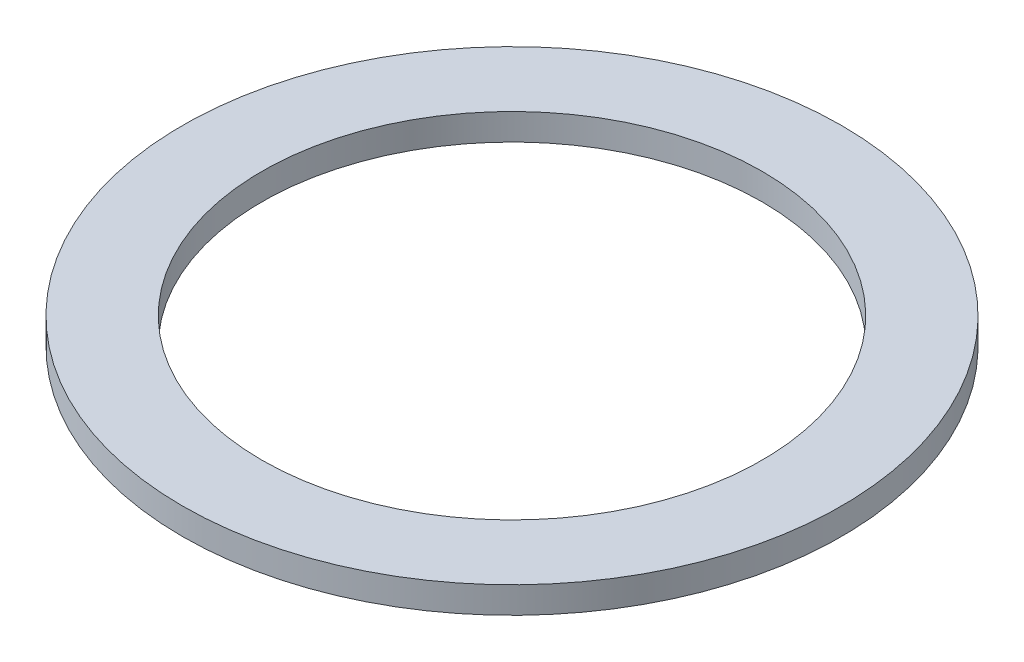
SolidWorks part; units mm, degrees
ref_plane "Front Plane" through (0, 0, 0) normal (0, 0, 1) x (1, 0, 0)
ref_plane "Top Plane" through (0, 0, 0) normal (0, 1, 0) x (1, 0, 0)
ref_plane "Right Plane" through (0, 0, 0) normal (1, 0, 0) x (0, 0, -1)
sketch "Sketch1" plane through (0, 0, 0) normal (0, 1, 0) x (1, 0, 0)
  circle A0 centre (0, 0) radius 6.3246
  dimension "OD" = 12.6492
extrude "Boss-Extrude1" add sketch "Sketch1" along normal blind 0.508
sketch "Sketch5" plane through (0, 0.508, 0) normal (0, 1, 0) x (-1, 0, 0)
  circle A0 centre (0, 0) radius 4.8006
  dimension "ID" = 9.6012
extrude "Cut-Extrude1" cut sketch "Sketch5" against normal through all
